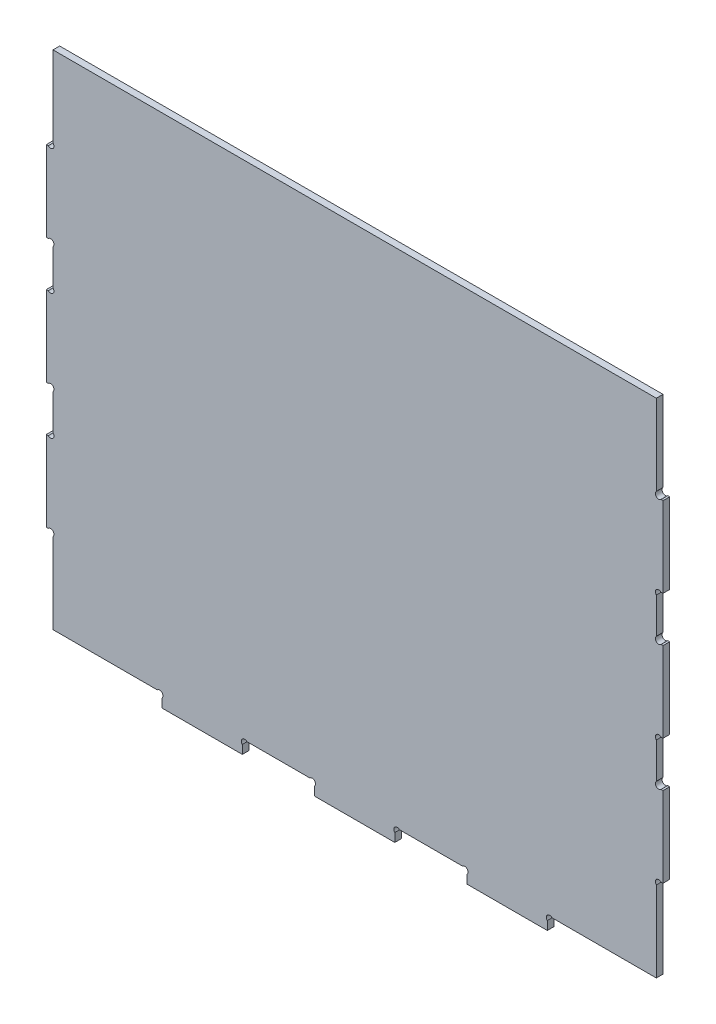
SolidWorks part; units mm, degrees
material "6061-T6 (SS)"
ref_plane "Front" through (0, 0, 0) normal (0, 0, 1) x (1, 0, 0)
ref_plane "Top" through (0, 0, 0) normal (0, 1, 0) x (1, 0, 0)
ref_plane "Right" through (0, 0, 0) normal (1, 0, 0) x (0, 0, -1)
sketch "Sketch2" plane through (0, 0, 0) normal (0, 0, 1) x (1, 0, 0)
  line L0 (-289.475, 241.45) -> (-289.475, 0) construction
  line L1 (0, 0) -> (-289.475, 0) construction
  line L6 (0, 241.45) -> (-289.475, 241.45) construction
  line L7 (-289.475, 241.45) -> (-289.475, 0) construction
  line L8 (0, 0) -> (-289.475, 0) construction
  line L13 (0, 241.45) -> (-289.475, 241.45) construction
  line L17 (-287.8875, 3.175) -> (-287.8875, 241.45)
  line L19 (-287.8875, 3.175) -> (-1.5875, 3.175)
  line L20 (-144.7375, 3.175) -> (-144.7375, 241.45) construction
  line L21 (-287.8875, 241.45) -> (-1.5875, 241.45)
  line L22 (-1.5875, 3.175) -> (-1.5875, 241.45)
  point P6 (-144.7375, 0)
  dimension "D2" = 3.175
  dimension "D1" = 1.5875
extrude "Boss-Extrude1" add sketch "Sketch2" along normal mid plane 3.175
sketch "Sketch4" plane through (0, 0, -1.5875) normal (0, 0, -1) x (-1, 0, 0)
  line L0 (1.5875, 3.175) -> (1.5875, 241.45) construction
  line L1 (-1.5875, 200.9312) -> (1.5875, 200.9312)
  line L2 (-1.5875, 200.9312) -> (-1.5875, 162.8312)
  line L3 (-1.5875, 162.8312) -> (1.5875, 162.8312)
  line L4 (1.5875, 200.9312) -> (1.5875, 162.8312)
  line L5 (-1.5875, 200.9312) -> (1.5875, 162.8312) construction
  line L6 (-1.5875, 162.8312) -> (1.5875, 200.9312) construction
  line L7 (287.8875, 3.175) -> (1.5875, 3.175) construction
  line L8 (-1.5875, 141.3625) -> (1.5875, 141.3625)
  line L9 (-1.5875, 141.3625) -> (-1.5875, 103.2625)
  line L10 (-1.5875, 103.2625) -> (1.5875, 103.2625)
  line L11 (1.5875, 141.3625) -> (1.5875, 103.2625)
  line L12 (-1.5875, 141.3625) -> (1.5875, 103.2625) construction
  line L13 (-1.5875, 103.2625) -> (1.5875, 141.3625) construction
  line L14 (-1.5875, 81.7937) -> (1.5875, 81.7937)
  line L15 (-1.5875, 81.7937) -> (-1.5875, 43.6937)
  line L16 (-1.5875, 43.6937) -> (1.5875, 43.6937)
  line L17 (1.5875, 81.7937) -> (1.5875, 43.6937)
  line L18 (-1.5875, 81.7937) -> (1.5875, 43.6937) construction
  line L19 (-1.5875, 43.6937) -> (1.5875, 81.7937) construction
  line L20 (53.3188, -3.175) -> (91.4188, -3.175)
  line L21 (53.3188, -3.175) -> (53.3188, 3.175)
  line L22 (53.3188, 3.175) -> (91.4188, 3.175)
  line L23 (91.4188, -3.175) -> (91.4188, 3.175)
  line L24 (53.3188, -3.175) -> (91.4188, 3.175) construction
  line L25 (53.3188, 3.175) -> (91.4188, -3.175) construction
  line L26 (287.8875, 241.45) -> (287.8875, 3.175) construction
  line L27 (125.6875, -3.175) -> (163.7875, -3.175)
  line L28 (125.6875, -3.175) -> (125.6875, 3.175)
  line L29 (125.6875, 3.175) -> (163.7875, 3.175)
  line L30 (163.7875, -3.175) -> (163.7875, 3.175)
  line L31 (125.6875, -3.175) -> (163.7875, 3.175) construction
  line L32 (125.6875, 3.175) -> (163.7875, -3.175) construction
  line L33 (198.0563, -3.175) -> (236.1563, -3.175)
  line L34 (198.0563, -3.175) -> (198.0563, 3.175)
  line L35 (198.0563, 3.175) -> (236.1563, 3.175)
  line L36 (236.1563, -3.175) -> (236.1563, 3.175)
  line L37 (198.0563, -3.175) -> (236.1563, 3.175) construction
  line L38 (198.0563, 3.175) -> (236.1563, -3.175) construction
  line L39 (291.0625, 200.9312) -> (287.8875, 200.9312)
  line L40 (291.0625, 200.9312) -> (291.0625, 162.8312)
  line L41 (291.0625, 162.8312) -> (287.8875, 162.8312)
  line L42 (287.8875, 200.9312) -> (287.8875, 162.8312)
  line L43 (291.0625, 200.9312) -> (287.8875, 162.8312) construction
  line L44 (291.0625, 162.8312) -> (287.8875, 200.9312) construction
  line L46 (291.0625, 141.3625) -> (287.8875, 141.3625)
  line L47 (291.0625, 141.3625) -> (291.0625, 103.2625)
  line L48 (291.0625, 103.2625) -> (287.8875, 103.2625)
  line L49 (287.8875, 141.3625) -> (287.8875, 103.2625)
  line L50 (291.0625, 141.3625) -> (287.8875, 103.2625) construction
  line L51 (291.0625, 103.2625) -> (287.8875, 141.3625) construction
  line L52 (291.0625, 81.7937) -> (287.8875, 81.7937)
  line L53 (291.0625, 81.7937) -> (291.0625, 43.6937)
  line L54 (291.0625, 43.6937) -> (287.8875, 43.6937)
  line L55 (287.8875, 81.7937) -> (287.8875, 43.6937)
  line L56 (291.0625, 81.7937) -> (287.8875, 43.6937) construction
  line L57 (291.0625, 43.6937) -> (287.8875, 81.7937) construction
  point P0 (0, 181.8812)
  point P2 (0, 122.3125)
  point P4 (0, 62.7437)
  point P6 (289.475, 62.7437)
  point P8 (289.475, 122.3125)
  point P10 (289.475, 181.8812)
  point P12 (72.3688, 0)
  point P14 (144.7375, 0)
  point P16 (217.1063, 0)
  point P18 (0, 181.8812)
  point P25 (0, 122.3125)
  point P30 (0, 62.7437)
  point P35 (72.3688, 0)
  point P42 (144.7375, 0)
  point P47 (217.1063, 0)
  point P52 (289.475, 181.8812)
  point P59 (289.475, 122.3125)
  point P64 (289.475, 62.7437)
  dimension "D1" = 38.1
extrude "Weld Tabs Extrude" add sketch "Sketch4" against normal up to surface (3.175 mm away) up to face at (-144.7375, 122.3125, 1.5875)
sketch "Sketch5" plane through (0, 0, 1.5875) normal (0, 0, 1) x (1, 0, 0)
  line L0 (-1.5875, 141.3625) -> (-0.465, 141.3625) construction
  line L1 (-1.5875, 200.9312) -> (-0.465, 200.9312) construction
  line L2 (-1.5875, 200.9312) -> (-1.5875, 202.0538) construction
  line L3 (-1.5875, 202.0538) -> (-0.465, 202.0538) construction
  line L4 (-0.465, 200.9312) -> (-0.465, 202.0538) construction
  line L5 (-1.5875, 141.3625) -> (-1.5875, 142.485) construction
  line L6 (-1.5875, 142.485) -> (-0.465, 142.485) construction
  line L7 (-0.465, 141.3625) -> (-0.465, 142.485) construction
  line L8 (-1.5875, 81.7937) -> (-0.465, 81.7937) construction
  line L9 (-1.5875, 81.7937) -> (-1.5875, 82.9163) construction
  line L10 (-1.5875, 82.9163) -> (-0.465, 82.9163) construction
  line L11 (-0.465, 81.7937) -> (-0.465, 82.9163) construction
  line L12 (-1.5875, 103.2625) -> (-0.465, 103.2625) construction
  line L13 (-1.5875, 162.8312) -> (-0.465, 162.8312) construction
  line L14 (-1.5875, 162.8312) -> (-1.5875, 161.7087) construction
  line L15 (-1.5875, 161.7087) -> (-0.465, 161.7087) construction
  line L16 (-0.465, 162.8312) -> (-0.465, 161.7087) construction
  line L17 (-1.5875, 103.2625) -> (-1.5875, 102.14) construction
  line L18 (-1.5875, 102.14) -> (-0.465, 102.14) construction
  line L19 (-0.465, 103.2625) -> (-0.465, 102.14) construction
  line L20 (-1.5875, 43.6937) -> (-0.465, 43.6938) construction
  line L21 (-1.5875, 43.6937) -> (-1.5875, 42.5712) construction
  line L22 (-1.5875, 42.5712) -> (-0.465, 42.5712) construction
  line L23 (-0.465, 43.6938) -> (-0.465, 42.5712) construction
  line L24 (-144.7375, 241.45) -> (-144.7375, -3.175) construction
  line L26 (-53.3188, 3.175) -> (-52.1962, 3.175) construction
  line L27 (-53.3188, 3.175) -> (-53.3188, 2.0525) construction
  line L28 (-53.3188, 2.0525) -> (-52.1962, 2.0525) construction
  line L29 (-52.1962, 3.175) -> (-52.1962, 2.0525) construction
  line L30 (-125.6875, 3.175) -> (-124.565, 3.175) construction
  line L31 (-125.6875, 3.175) -> (-125.6875, 2.0525) construction
  line L32 (-125.6875, 2.0525) -> (-124.565, 2.0525) construction
  line L33 (-124.565, 3.175) -> (-124.565, 2.0525) construction
  line L34 (-91.4188, 3.175) -> (-92.5413, 3.175) construction
  line L35 (-91.4188, 3.175) -> (-91.4188, 2.0525) construction
  line L36 (-91.4188, 2.0525) -> (-92.5413, 2.0525) construction
  line L37 (-92.5413, 3.175) -> (-92.5413, 2.0525) construction
  line L40 (-1.5875, 241.45) -> (-287.8875, 241.45)
  line L41 (-287.8875, 241.45) -> (-287.8875, 200.9312)
  line L42 (-287.8875, 200.9312) -> (-291.0625, 200.9312)
  line L43 (-291.0625, 200.9312) -> (-291.0625, 162.8312)
  line L44 (-291.0625, 162.8312) -> (-287.8875, 162.8312)
  line L45 (-287.8875, 162.8312) -> (-287.8875, 141.3625)
  line L46 (-287.8875, 141.3625) -> (-291.0625, 141.3625)
  line L47 (-291.0625, 141.3625) -> (-291.0625, 103.2625)
  line L48 (-291.0625, 103.2625) -> (-287.8875, 103.2625)
  line L49 (-287.8875, 103.2625) -> (-287.8875, 81.7937)
  line L50 (-287.8875, 81.7937) -> (-291.0625, 81.7937)
  line L51 (-291.0625, 81.7937) -> (-291.0625, 43.6937)
  line L52 (-291.0625, 43.6937) -> (-287.8875, 43.6937)
  line L53 (-287.8875, 43.6937) -> (-287.8875, 3.175)
  line L54 (-287.8875, 3.175) -> (-236.1563, 3.175)
  line L55 (-236.1563, 3.175) -> (-236.1563, -3.175)
  line L56 (-236.1563, -3.175) -> (-198.0563, -3.175)
  line L57 (-198.0563, -3.175) -> (-198.0563, 3.175)
  line L58 (-198.0563, 3.175) -> (-163.7875, 3.175)
  line L59 (-163.7875, 3.175) -> (-163.7875, -3.175)
  line L60 (-163.7875, -3.175) -> (-125.6875, -3.175)
  line L61 (-125.6875, -3.175) -> (-125.6875, 3.175)
  line L62 (-125.6875, 3.175) -> (-91.4188, 3.175)
  line L63 (-91.4188, 3.175) -> (-91.4188, -3.175)
  line L64 (-91.4188, -3.175) -> (-53.3188, -3.175)
  line L65 (-53.3188, -3.175) -> (-53.3188, 3.175)
  line L66 (-53.3188, 3.175) -> (-1.5875, 3.175)
  line L67 (-1.5875, 3.175) -> (-1.5875, 43.6937)
  line L68 (-1.5875, 43.6937) -> (1.5875, 43.6937)
  line L69 (1.5875, 43.6937) -> (1.5875, 81.7937)
  line L70 (1.5875, 81.7937) -> (-1.5875, 81.7937)
  line L71 (-1.5875, 81.7937) -> (-1.5875, 103.2625)
  line L72 (-1.5875, 103.2625) -> (1.5875, 103.2625)
  line L73 (1.5875, 103.2625) -> (1.5875, 141.3625)
  line L74 (1.5875, 141.3625) -> (-1.5875, 141.3625)
  line L75 (-1.5875, 141.3625) -> (-1.5875, 162.8312)
  line L76 (-1.5875, 162.8312) -> (1.5875, 162.8312)
  line L77 (1.5875, 162.8312) -> (1.5875, 200.9312)
  line L78 (1.5875, 200.9312) -> (-1.5875, 200.9312)
  line L79 (-1.5875, 200.9312) -> (-1.5875, 241.45)
  line L80 (-1.5875, 241.45) -> (-287.8875, 241.45) construction
  line L81 (-287.8875, 241.45) -> (-287.8875, 200.9312) construction
  line L82 (-287.8875, 200.9312) -> (-291.0625, 200.9312) construction
  line L83 (-291.0625, 200.9312) -> (-291.0625, 162.8312) construction
  line L84 (-291.0625, 162.8312) -> (-287.8875, 162.8312) construction
  line L85 (-287.8875, 162.8312) -> (-287.8875, 141.3625) construction
  line L86 (-287.8875, 141.3625) -> (-291.0625, 141.3625) construction
  line L87 (-291.0625, 141.3625) -> (-291.0625, 103.2625) construction
  line L88 (-291.0625, 103.2625) -> (-287.8875, 103.2625) construction
  line L89 (-287.8875, 103.2625) -> (-287.8875, 81.7937) construction
  line L90 (-287.8875, 81.7937) -> (-291.0625, 81.7937) construction
  line L91 (-291.0625, 81.7937) -> (-291.0625, 43.6937) construction
  line L92 (-291.0625, 43.6937) -> (-287.8875, 43.6937) construction
  line L93 (-287.8875, 43.6937) -> (-287.8875, 3.175) construction
  line L94 (-287.8875, 3.175) -> (-236.1563, 3.175) construction
  line L95 (-236.1563, 3.175) -> (-236.1563, -3.175) construction
  line L96 (-236.1563, -3.175) -> (-198.0563, -3.175) construction
  line L97 (-198.0563, -3.175) -> (-198.0563, 3.175) construction
  line L98 (-198.0563, 3.175) -> (-163.7875, 3.175) construction
  line L99 (-163.7875, 3.175) -> (-163.7875, -3.175) construction
  line L100 (-163.7875, -3.175) -> (-125.6875, -3.175) construction
  line L101 (-125.6875, -3.175) -> (-125.6875, 3.175) construction
  line L102 (-125.6875, 3.175) -> (-91.4188, 3.175) construction
  line L103 (-91.4188, 3.175) -> (-91.4188, -3.175) construction
  line L104 (-91.4188, -3.175) -> (-53.3188, -3.175) construction
  line L105 (-53.3188, -3.175) -> (-53.3188, 3.175) construction
  line L106 (-53.3188, 3.175) -> (-1.5875, 3.175) construction
  line L107 (-1.5875, 3.175) -> (-1.5875, 43.6937) construction
  line L108 (-1.5875, 43.6937) -> (1.5875, 43.6937) construction
  line L109 (1.5875, 43.6937) -> (1.5875, 81.7937) construction
  line L110 (1.5875, 81.7937) -> (-1.5875, 81.7937) construction
  line L111 (-1.5875, 81.7937) -> (-1.5875, 103.2625) construction
  line L112 (-1.5875, 103.2625) -> (1.5875, 103.2625) construction
  line L113 (1.5875, 103.2625) -> (1.5875, 141.3625) construction
  line L114 (1.5875, 141.3625) -> (-1.5875, 141.3625) construction
  line L115 (-1.5875, 141.3625) -> (-1.5875, 162.8312) construction
  line L116 (-1.5875, 162.8312) -> (1.5875, 162.8312) construction
  line L117 (1.5875, 162.8312) -> (1.5875, 200.9312) construction
  line L118 (1.5875, 200.9312) -> (-1.5875, 200.9312) construction
  line L119 (-1.5875, 200.9312) -> (-1.5875, 241.45) construction
  circle A0 centre (-0.465, 202.0538) radius 1.5875
  circle A1 centre (-0.465, 142.485) radius 1.5875
  circle A2 centre (-0.465, 82.9163) radius 1.5875
  circle A3 centre (-0.465, 161.7087) radius 1.5875
  circle A4 centre (-0.465, 102.14) radius 1.5875
  circle A5 centre (-0.465, 42.5712) radius 1.5875
  circle A6 centre (-289.01, 42.5712) radius 1.5875
  circle A7 centre (-289.01, 82.9163) radius 1.5875
  circle A8 centre (-289.01, 102.14) radius 1.5875
  circle A9 centre (-289.01, 142.485) radius 1.5875
  circle A10 centre (-289.01, 161.7087) radius 1.5875
  circle A11 centre (-289.01, 202.0538) radius 1.5875
  circle A12 centre (-52.1962, 2.0525) radius 1.5875
  circle A13 centre (-92.5413, 2.0525) radius 1.5875
  circle A14 centre (-124.565, 2.0525) radius 1.5875
  circle A15 centre (-237.2788, 2.0525) radius 1.5875
  circle A16 centre (-196.9337, 2.0525) radius 1.5875
  circle A17 centre (-164.91, 2.0525) radius 1.5875
  dimension "D2" = 3.175
  dimension "D3" = 3
  dimension "D4" = 3
extrude "Cut-Extrude1" cut sketch "Sketch5" against normal up to surface (3.175 mm away)
equation "\"D1@Sketch4\"=\"weld slot length@FS2-EN-ACC-A-0003-V1, ACCUMULATOR CONTAINER.Assembly\""
equation "\"D1@Sketch2\"=\"acc rear wall thickness@FS2-EN-ACC-A-0003-V1, ACCUMULATOR CONTAINER.Assembly\"/2"
equation "\"D2@Sketch5\"=\"weld teardrop radius@FS2-EN-ACC-A-0003-V1, ACCUMULATOR CONTAINER.Assembly\"*2"
